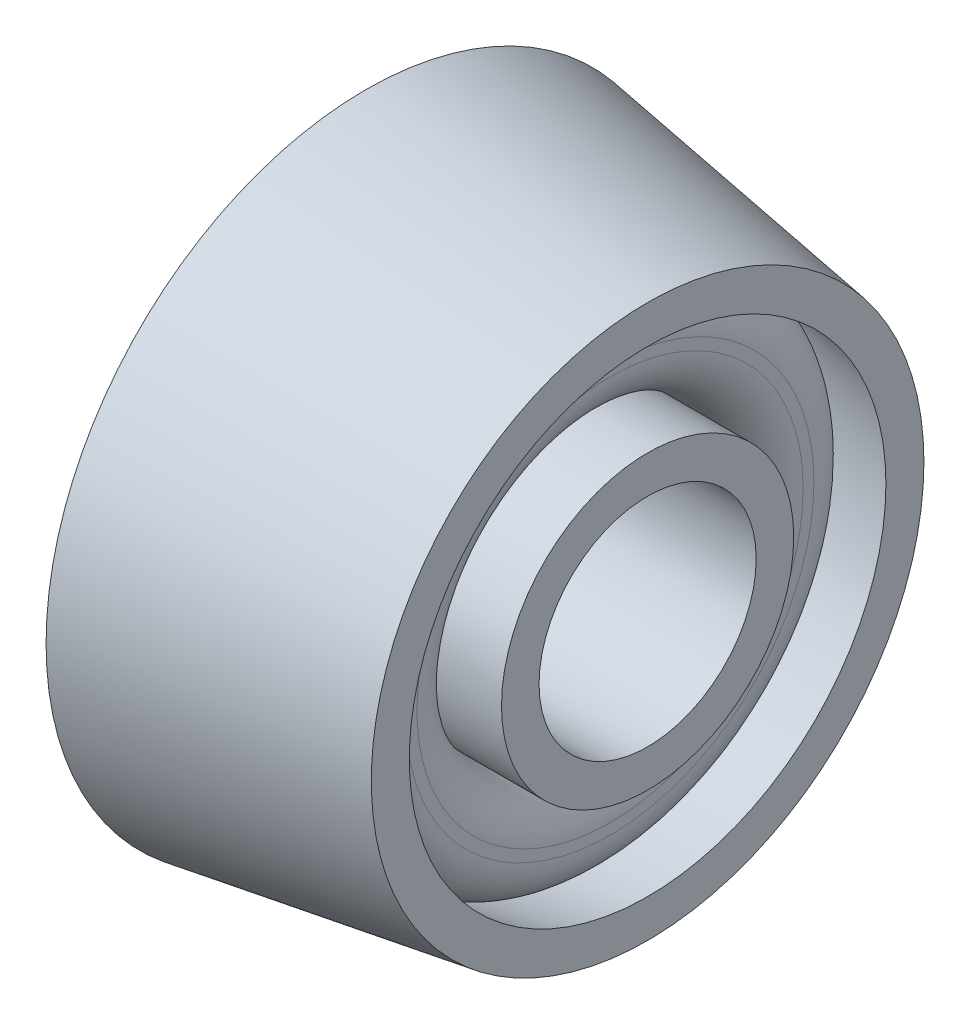
SolidWorks part; units mm, degrees
ref_plane "Front Plane" through (0, 0, 0) normal (0, 0, 1) x (1, 0, 0)
ref_plane "Top Plane" through (0, 0, 0) normal (0, 1, 0) x (1, 0, 0)
ref_plane "Right Plane" through (0, 0, 0) normal (1, 0, 0) x (0, 0, -1)
sketch "Sketch1" plane through (0, 0, 0) normal (0, 1, 0) x (1, 0, 0)
  line L2 (882.163, 111.9961) -> (882.163, 90.3656)
  line L3 (901.213, 109.0514) -> (901.213, 90.3656)
  line L4 (882.163, 111.9961) -> (901.213, 109.0514)
  line L5 (1002.1119, 90.3656) -> (927.1762, 90.3656) construction
  line L6 (882.163, 90.3656) -> (901.213, 90.3656)
  spline S0 degree 3 poles (1651.2448, -552.3436) (1465.7468, -14.0861) (1163.9718, 72.3029) (840.2093, 118.0427) (824.9254, 120.0929) (794.3342, 124.0303) (779.0268, 125.9171) (748.3946, 129.5549) (733.0696, 131.3056) (687.0737, 136.38) (656.382, 139.5276) (594.9594, 145.4266) (564.2282, 148.1772) (502.7347, 153.3061) (471.9722, 155.6844) (410.421, 160.059) (379.6323, 162.0562) (333.4324, 164.7252) (318.0296, 165.56) (287.2191, 167.105) (271.8113, 167.8155) (240.992, 169.0846) (225.5804, 169.645) (202.4632, 170.325) (194.7574, 170.5252) (183.2016, 170.7673) (179.35, 170.8382) (51.7504, 172.7403) (-71.5659, 164.9445) (298.9024, -819.7445) knots -1.200454 -1.200454 -1.200454 -1.200454 0.0625 0.0625 0.125 0.125 0.1875 0.1875 0.25 0.25 0.375 0.375 0.5 0.5 0.625 0.625 0.75 0.75 0.8125 0.8125 0.875 0.875 0.9375 0.9375 0.96875 0.96875 0.984375 0.984375 1.48656 1.48656 1.48656 1.48656 only from (901.213, 109.0514) to (163.9648, 171.0106) construction
  spline S1 degree 3 poles (901.213, 109.0514) (885.9926, 111.4675) (870.7425, 113.7291) (840.2093, 118.0427) (824.9254, 120.0929) (794.3342, 124.0303) (779.0268, 125.9171) (748.3946, 129.5549) (733.0696, 131.3056) (687.0737, 136.38) (656.382, 139.5276) (594.9594, 145.4266) (564.2282, 148.1772) (502.7347, 153.3061) (471.9722, 155.6844) (410.421, 160.059) (379.6323, 162.0562) (333.4324, 164.7252) (318.0296, 165.56) (287.2191, 167.105) (271.8113, 167.8155) (240.992, 169.0846) (225.5804, 169.645) (202.4632, 170.325) (194.7574, 170.5252) (183.2016, 170.7673) (179.35, 170.8382) (171.6493, 170.953) (167.7994, 171.001) (163.9648, 171.0106) knots 0 0 0 0 0.0625 0.0625 0.125 0.125 0.1875 0.1875 0.25 0.25 0.375 0.375 0.5 0.5 0.625 0.625 0.75 0.75 0.8125 0.8125 0.875 0.875 0.9375 0.9375 0.96875 0.96875 0.984375 0.984375 1 1 1 1 construction
  point P5 (1002.1119, 90.3656)
  dimension "D1" = 19.05
revolve "Revolve2" add sketch "Sketch1" angle 360 about L5
hole_wizard "Tapped Hole for 9/16-12 Helicoil1" positions "Sketch2" profile "Sketch3" tap size "9/16-12" standard "Helicoil® Inch" end condition through all
sketch "Sketch2" plane through (882.163, 0, 0) normal (-1, 0, 0) x (0, 0, 1)
  circle A3 centre (-90.3656, 0) radius 21.6305
  circle A4 centre (-90.3656, 0) radius 21.6305 construction
  point P0 (-90.3656, 0)
  dimension "D1" = 0
cosmetic thread "Hole Thread1" parameters "D1"=19.05, "D2"=17.1475
sketch "Sketch3" plane through (882.163, 0, -90.3656) normal (0, 1, 0) x (0, 0, 1)
  line L0 (0, 0) -> (0, 19.05)
  line L1 (0, 19.05) -> (7.3419, 19.05)
  line L2 (7.3419, 19.05) -> (7.3419, 0)
  line L5 (7.3419, 0) -> (0, 0)
  line L11 (0, -6.35) -> (0, 107.95) construction
  dimension "Thru Tap Drill Dia." = 14.6837
  dimension "Thru Tap Drill Depth" = 19.05
sketch "Sketch4" plane through (882.163, 0, 0) normal (-1, 0, 0) x (0, 0, 1)
  circle A0 centre (-90.3656, 0) radius 10.3187
  circle A1 centre (-90.3656, 0) radius 19.05
  dimension "D1" = 20.6375
  dimension "D2" = 38.1
extrude "Cut-Extrude1" [suppressed] cut sketch "Sketch4" against normal blind 12.7 draft 10
fillet "Fillet1" [suppressed] radius 3.175
sketch "Sketch5" plane through (0, 0, 0) normal (0, 1, 0) x (1, 0, 0)
  line L1 (928.6367, 102.2422) -> (928.6367, 100.2475)
  line L2 (928.6367, 102.2422) -> (895.983, 107.2897)
  line L5 (898.673, 104.152) -> (898.673, 103.4225)
  line L6 (895.498, 100.2475) -> (928.6367, 100.2475)
  line L7 (901.213, 109.0514) -> (882.163, 111.9961) construction
  line L8 (901.213, 109.0514) -> (882.163, 111.9961) construction
  line L9 (901.213, 97.7075) -> (882.163, 97.7075) construction
  line L10 (901.213, 97.7075) -> (882.163, 97.7075) construction
  line L12 (1002.1119, 90.3656) -> (913.4307, 90.3656) construction
  arc A0 (898.673, 103.4225) -> (895.498, 100.2475) centre (895.498, 103.4225) cw
  arc A1 (895.983, 107.2897) -> (898.673, 104.152) centre (895.498, 104.152) cw
  point P14 (898.673, 106.8739)
  dimension "D5" = 3.175
  dimension "D2" = 2.54
  dimension "D4" = 2.54
  dimension "D1" = 2.54
revolve "Cut-Revolve1" cut sketch "Sketch5" angle 360 about L12
